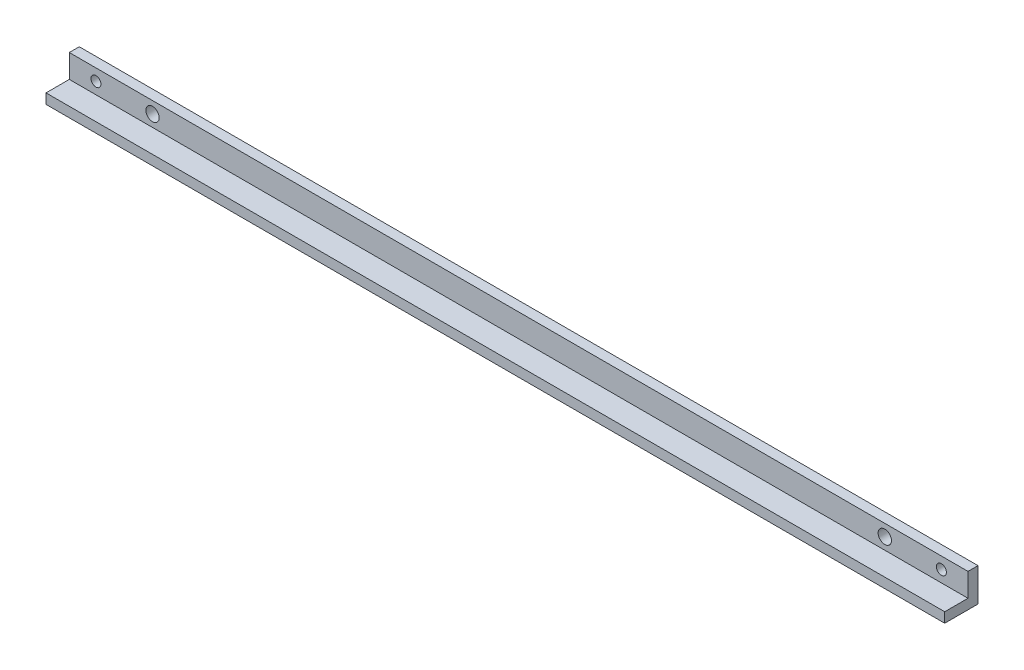
SolidWorks part; units mm, degrees
ref_plane "Спереди" through (0, 0, 0) normal (0, 0, 1) x (1, 0, 0)
ref_plane "Сверху" through (0, 0, 0) normal (0, 1, 0) x (1, 0, 0)
ref_plane "Справа" through (0, 0, 0) normal (1, 0, 0) x (0, 0, -1)
sketch "Эскиз1" plane through (0, 0, 0) normal (1, 0, 0) x (0, 0, -1)
  line L0 (0, 0) -> (-10, 0)
  line L1 (-10, 0) -> (-10, 3)
  line L2 (-10, 3) -> (-3, 3)
  line L3 (-3, 10) -> (-3, 3)
  line L6 (-3, 10) -> (0, 10)
  line L7 (0, 10) -> (0, 0)
  dimension "D1" = 3
  dimension "D2" = 10
extrude "Бобышка-Вытянуть1" add sketch "Эскиз1" along normal blind 270
sketch "Эскиз2" plane through (0, 0, 3) normal (0, 0, 1) x (1, 0, 0)
  line L0 (135, 10) -> (135, 3) construction
  line L1 (270, 10) -> (0, 10) construction
  line L2 (270, 3) -> (0, 3) construction
  line L3 (0, 10) -> (0, 3) construction
  circle A0 centre (25, 6.5) radius 2
  circle A1 centre (245, 6.5) radius 2
  dimension "D1" = 4
  dimension "D2" = 25
extrude "Вырез-Вытянуть1" cut sketch "Эскиз2" against normal through all
sketch "Эскиз5" plane through (0, 0, 3) normal (0, 0, 1) x (1, 0, 0)
  line L0 (0, 10) -> (0, 3) construction
  line L2 (270, 10) -> (0, 10) construction
  line L3 (135, 10) -> (135, 0) construction
  line L4 (270, 0) -> (0, 0) construction
  circle A0 centre (8, 6.5) radius 1.5
  circle A1 centre (262, 6.5) radius 1.5
  dimension "D1" = 3
  dimension "D2" = 8
  dimension "D3" = 3.5
extrude "Вырез-Вытянуть2" cut sketch "Эскиз5" against normal through all
